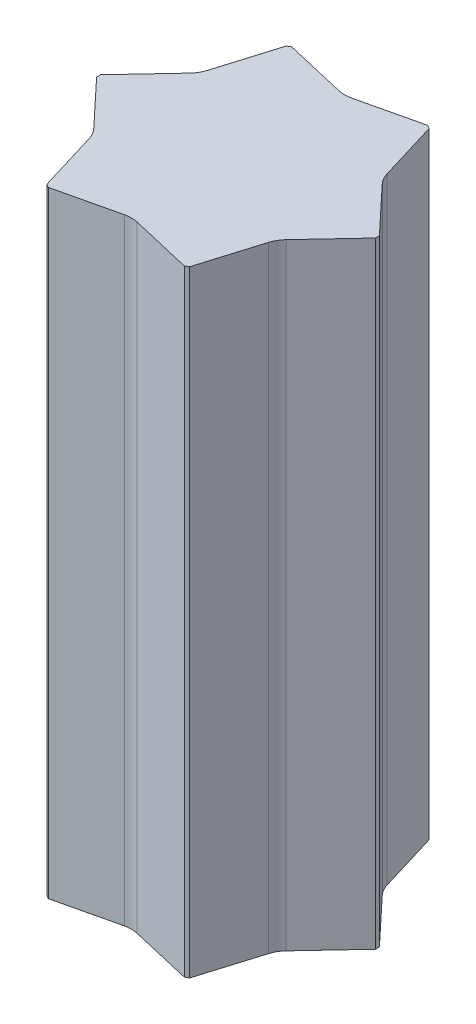
SolidWorks part; units mm, degrees
material "PEN"
ref_plane "前视基准面" through (0, 0, 0) normal (0, 0, 1) x (1, 0, 0)
ref_plane "上视基准面" through (0, 0, 0) normal (0, 1, 0) x (1, 0, 0)
ref_plane "右视基准面" through (0, 0, 0) normal (1, 0, 0) x (0, 0, -1)
sketch "草图2" plane through (0, 0, 0) normal (0, 1, 0) x (1, 0, 0)
  line L1 (345, 8.6603) -> (180, 294.4486)
  line L2 (165, 303.1089) -> (-165, 303.1089)
  line L3 (-180, 294.4486) -> (-345, 8.6603)
  line L4 (-345, -8.6603) -> (-180, -294.4486)
  line L5 (-165, -303.1089) -> (165, -303.1089)
  line L6 (180, -294.4486) -> (345, -8.6603)
  line L8 (-180, 294.4486) -> (-165, 303.1089)
  line L19 (165, 303.1089) -> (180, 294.4486)
  line L20 (345, 8.6603) -> (345, -8.6603)
  line L21 (165, -303.1089) -> (180, -294.4486)
  line L22 (-180, -294.4486) -> (-165, -303.1089)
  line L23 (-345, 8.6603) -> (-345, -8.6603)
  circle A0 centre (0, 0) radius 303.1089 construction
sketch "草图4" plane through (0, 0, 0) normal (0, 1, 0) x (1, 0, 0)
  line L0 (-165, 323.1172) -> (-165, 283.3064)
  line L1 (165, 303.1089) -> (-165, 303.1089) construction
  line L9 (165, 303.1089) -> (165, 323.0131)
  line L10 (165, 303.1089) -> (165, 283.2046)
  line L15 (-12.996, 247.6102) -> (-165, 283.3064)
  line L16 (-165, 323.1172) -> (-12.996, 358.6076)
  line L17 (12.996, 358.6076) -> (165, 323.0131)
  line L18 (165, 283.2046) -> (12.996, 247.6102)
  arc A3 (-12.996, 358.6076) -> (12.996, 358.6076) centre (0, 303.1089) cw
  arc A4 (12.996, 247.6102) -> (-12.996, 247.6102) centre (0, 303.1089) cw
sketch "草图5" plane through (0, 0, 0) normal (0, 1, 0) x (1, 0, 0)
  line L36 (238.2174, 122.5284) -> (345, 8.6603)
  line L37 (225.2214, 145.0381) -> (180, 294.4486)
  line L38 (180, 294.4486) -> (214.9693, 314.6382)
  line L39 (321.3479, 200.5368) -> (214.9693, 314.6382)
  line L40 (334.3439, 178.0271) -> (379.5202, 28.5905)
  line L41 (379.5202, 28.5905) -> (345, 8.6603)
  line L42 (225.2214, -145.0381) -> (180, -294.4486)
  line L43 (238.2174, -122.5284) -> (345, -8.6603)
  line L44 (12.996, 267.5665) -> (165, 303.1089)
  line L45 (-12.996, 267.5665) -> (-165, 303.1089)
  line L46 (-12.996, 378.5639) -> (-165, 343.488)
  line L47 (12.996, 378.5639) -> (165, 342.9694)
  line L48 (165, 342.9694) -> (165, 303.1089)
  line L49 (-165, 303.1089) -> (-165, 343.488)
  line L50 (345, -8.6603) -> (379.9693, -28.8498)
  line L51 (334.3439, -178.0271) -> (379.9693, -28.8498)
  line L52 (321.3479, -200.5368) -> (214.5202, -314.3789)
  line L53 (214.5202, -314.3789) -> (180, -294.4486)
  line L54 (-12.996, -267.5665) -> (-165, -303.1089)
  line L55 (12.996, -267.5665) -> (165, -303.1089)
  line L56 (165, -303.1089) -> (165, -343.488)
  line L57 (12.996, -378.5639) -> (165, -343.488)
  line L58 (-12.996, -378.5639) -> (-165, -342.9694)
  line L59 (-165, -342.9694) -> (-165, -303.1089)
  line L60 (-238.2174, -122.5284) -> (-345, -8.6603)
  line L61 (-225.2214, -145.0381) -> (-180, -294.4486)
  line L62 (-180, -294.4486) -> (-214.9693, -314.6382)
  line L63 (-321.3479, -200.5368) -> (-214.9693, -314.6382)
  line L64 (-334.3439, -178.0271) -> (-379.5202, -28.5905)
  line L65 (-379.5202, -28.5905) -> (-345, -8.6603)
  line L66 (-225.2214, 145.0381) -> (-180, 294.4486)
  line L67 (-238.2174, 122.5284) -> (-345, 8.6603)
  line L68 (-345, 8.6603) -> (-379.9693, 28.8498)
  line L69 (-334.3439, 178.0271) -> (-379.9693, 28.8498)
  line L70 (-321.3479, 200.5368) -> (-214.5202, 314.3789)
  line L71 (-214.5202, 314.3789) -> (-180, 294.4486)
  arc A13 (-12.996, 378.5639) -> (12.996, 378.5639) centre (0, 323.0652) cw
  arc A14 (-12.996, 267.5665) -> (12.996, 267.5665) centre (0, 323.0652) ccw
  arc A15 (225.2214, 145.0381) -> (238.2174, 122.5284) centre (279.7826, 161.5326) ccw
  arc A16 (321.3479, 200.5368) -> (334.3439, 178.0271) centre (279.7826, 161.5326) cw
  arc A17 (238.2174, -122.5284) -> (225.2214, -145.0381) centre (279.7826, -161.5326) ccw
  arc A18 (334.3439, -178.0271) -> (321.3479, -200.5368) centre (279.7826, -161.5326) cw
  arc A19 (12.996, -267.5665) -> (-12.996, -267.5665) centre (0, -323.0652) ccw
  arc A20 (12.996, -378.5639) -> (-12.996, -378.5639) centre (0, -323.0652) cw
  arc A21 (-225.2214, -145.0381) -> (-238.2174, -122.5284) centre (-279.7826, -161.5326) ccw
  arc A22 (-321.3479, -200.5368) -> (-334.3439, -178.0271) centre (-279.7826, -161.5326) cw
  arc A23 (-238.2174, 122.5284) -> (-225.2214, 145.0381) centre (-279.7826, 161.5326) ccw
  arc A24 (-334.3439, 178.0271) -> (-321.3479, 200.5368) centre (-279.7826, 161.5326) cw
  dimension "D1" = 6
sketch "草图7" plane through (0, 0, 0) normal (0, 1, 0) x (1, 0, 0)
  line L236 (-163.4254, 292.471) -> (-171.5746, 287.766)
  line L237 (-171.5746, 287.766) -> (-215.6492, 142.1443)
  line L238 (-230.923, 115.6879) -> (-335, 4.7049)
  line L239 (-335, 4.7049) -> (-335, -4.7049)
  line L240 (-335, -4.7049) -> (-230.9252, -115.6855)
  line L241 (-215.6502, -142.1412) -> (-171.5746, -287.766)
  line L242 (-171.5746, -287.766) -> (-163.4254, -292.471)
  line L243 (-163.4254, -292.471) -> (-15.276, -257.8299)
  line L244 (15.2728, -257.8291) -> (163.4254, -292.471)
  line L245 (163.4254, -292.471) -> (171.5746, -287.766)
  line L246 (171.5746, -287.766) -> (215.6492, -142.1443)
  line L247 (230.923, -115.6879) -> (335, -4.7049)
  line L248 (335, -4.7049) -> (335, 4.7049)
  line L249 (335, 4.7049) -> (230.9252, 115.6855)
  line L250 (171.5746, 287.766) -> (163.4254, 292.471)
  line L251 (215.6502, 142.1412) -> (171.5746, 287.766)
  line L252 (163.4254, 292.471) -> (15.276, 257.8299)
  line L253 (-15.2728, 257.8291) -> (-163.4254, 292.471)
  line L254 (-163.4254, 292.471) -> (-171.5746, 287.766)
  line L255 (-171.5746, 287.766) -> (-215.6492, 142.1443)
  line L256 (-230.923, 115.6879) -> (-335, 4.7049)
  line L257 (-335, 4.7049) -> (-335, -4.7049)
  line L258 (-335, -4.7049) -> (-230.9252, -115.6855)
  line L259 (-215.6502, -142.1412) -> (-171.5746, -287.766)
  line L260 (-171.5746, -287.766) -> (-163.4254, -292.471)
  line L261 (-163.4254, -292.471) -> (-15.276, -257.8299)
  line L262 (15.2728, -257.8291) -> (163.4254, -292.471)
  line L263 (163.4254, -292.471) -> (171.5746, -287.766)
  line L264 (171.5746, -287.766) -> (215.6492, -142.1443)
  line L265 (230.923, -115.6879) -> (335, -4.7049)
  line L266 (335, -4.7049) -> (335, 4.7049)
  line L267 (335, 4.7049) -> (230.9252, 115.6855)
  line L268 (171.5746, 287.766) -> (163.4254, 292.471)
  line L269 (215.6502, 142.1412) -> (171.5746, 287.766)
  line L270 (163.4254, 292.471) -> (15.276, 257.8299)
  line L271 (-15.2728, 257.8291) -> (-163.4254, 292.471)
  arc A82 (-230.923, 115.6879) -> (-215.6492, 142.1443) centre (-279.7826, 161.5326) ccw
  arc A83 (-215.6502, -142.1412) -> (-230.9252, -115.6855) centre (-279.7826, -161.5326) ccw
  arc A84 (15.2728, -257.8291) -> (-15.276, -257.8299) centre (0, -323.0652) ccw
  arc A85 (230.923, -115.6879) -> (215.6492, -142.1443) centre (279.7826, -161.5326) ccw
  arc A86 (215.6502, 142.1412) -> (230.9252, 115.6855) centre (279.7826, 161.5326) ccw
  arc A87 (-15.2728, 257.8291) -> (15.276, 257.8299) centre (0, 323.0652) ccw
  arc A88 (-230.923, 115.6879) -> (-215.6492, 142.1443) centre (-279.7826, 161.5326) ccw
  arc A89 (-215.6502, -142.1412) -> (-230.9252, -115.6855) centre (-279.7826, -161.5326) ccw
  arc A90 (15.2728, -257.8291) -> (-15.276, -257.8299) centre (0, -323.0652) ccw
  arc A91 (230.923, -115.6879) -> (215.6492, -142.1443) centre (279.7826, -161.5326) ccw
  arc A92 (215.6502, 142.1412) -> (230.9252, 115.6855) centre (279.7826, 161.5326) ccw
  arc A93 (-15.2728, 257.8291) -> (15.276, 257.8299) centre (0, 323.0652) ccw
  dimension "D1" = 10
extrude "凸台-拉伸1" add sketch "草图7" along normal blind 1480
